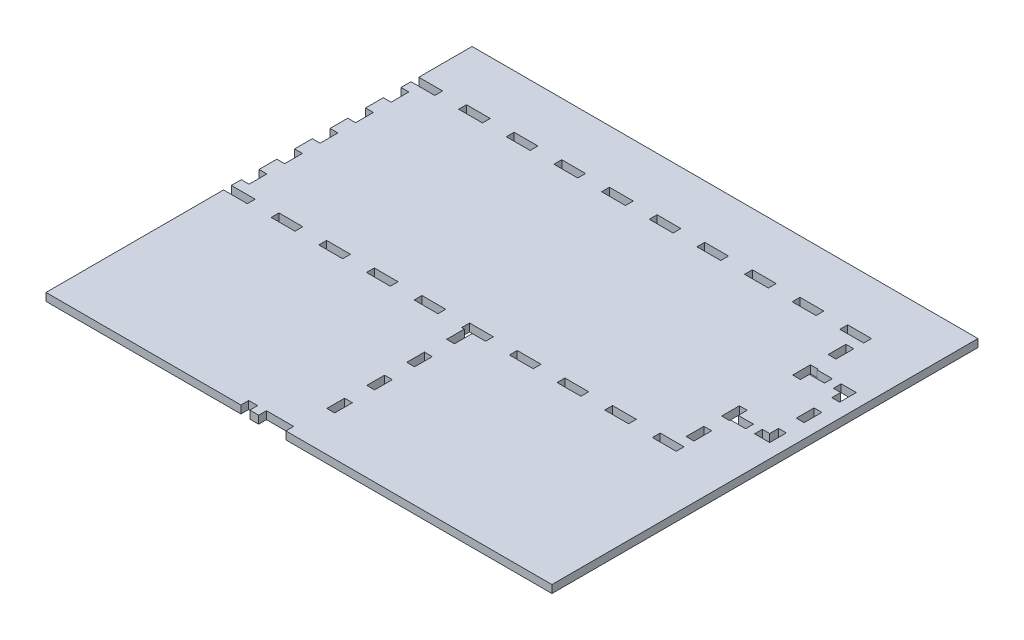
SolidWorks part; units mm, degrees
material "Acrylic (Medium-high impact)"
ref_plane "Front Plane" through (0, 0, 0) normal (0, 0, 1) x (1, 0, 0)
ref_plane "Top Plane" through (0, 0, 0) normal (0, 1, 0) x (1, 0, 0)
ref_plane "Right Plane" through (0, 0, 0) normal (1, 0, 0) x (0, 0, -1)
sketch "Sketch1" plane through (0, 0, 0) normal (0, 1, 0) x (1, 0, 0)
  line L1 (-161.925, 69.85) -> (161.925, 69.85)
  line L2 (-161.925, 69.85) -> (-161.925, -69.85)
  line L3 (-161.925, -69.85) -> (161.925, -69.85)
  line L4 (161.925, 69.85) -> (161.925, -69.85)
  point P4 (-161.925, 0)
  point P6 (0, 69.85)
  dimension "D1" = 139.7
  dimension "D2" = 323.85
extrude "Boss-Extrude1" add sketch "Sketch1" along normal blind 5.588
sketch "Sketch2" plane through (0, 5.588, 0) normal (0, 1, 0) x (1, 0, 0)
  line L0 (161.925, -69.85) -> (161.925, 69.85) construction
  line L1 (-161.925, 69.85) -> (161.925, 69.85)
  line L2 (-161.925, 69.85) -> (-161.925, -69.85)
  line L3 (-161.925, -69.85) -> (161.925, -69.85)
  line L4 (161.925, 69.85) -> (161.925, -69.85)
  line L5 (-161.925, -69.85) -> (161.925, -69.85) construction
  line L7 (-156.337, 64.262) -> (156.337, 64.262)
  line L8 (-156.337, 64.262) -> (-156.337, -64.262)
  line L9 (-156.337, -64.262) -> (156.337, -64.262)
  line L10 (156.337, 64.262) -> (156.337, -64.262)
  point P7 (-156.337, 0)
  point P14 (-161.925, 0)
  point P15 (0, -64.262)
  point P16 (0, -69.85)
  point P17 (156.337, 0)
  point P18 (161.925, 0)
  dimension "D1" = 5.588
  dimension "D2" = 5.588
extrude "Boss-Extrude2" add sketch "Sketch2" along normal blind 298.45
sketch "Sketch3" plane through (0, 0, 69.85) normal (0, 0, 1) x (1, 0, 0)
  line L0 (-51.435, 304.038) -> (-51.435, 0) construction
  line L2 (-156.337, 5.588) -> (156.337, 5.588) construction
  line L4 (-54.737, 282.448) -> (-54.737, 5.588)
  line L5 (-54.737, 5.588) -> (-48.133, 5.588)
  line L6 (-48.133, 291.592) -> (-48.133, 5.588)
  line L7 (-48.133, 291.592) -> (-67.691, 291.592)
  line L9 (-57.277, 284.988) -> (-67.691, 284.988)
  line L10 (-67.691, 291.592) -> (-67.691, 284.988)
  line L11 (-48.133, 101.6) -> (-35.433, 101.6) construction
  line L12 (-161.925, 0) -> (161.925, 0) construction
  line L13 (-38.608, 88.9) -> (-38.608, 101.6) construction
  line L14 (-41.783, 88.9) -> (-35.433, 88.9)
  line L15 (-41.783, 88.9) -> (-41.783, 71.9667)
  line L16 (-41.783, 71.9667) -> (-35.433, 71.9667)
  line L17 (-35.433, 88.9) -> (-35.433, 71.9667)
  line L18 (-41.783, 42.3333) -> (-35.433, 42.3333)
  line L19 (-41.783, 42.3333) -> (-41.783, 59.2667)
  line L20 (-41.783, 59.2667) -> (-35.433, 59.2667)
  line L21 (-35.433, 42.3333) -> (-35.433, 59.2667)
  line L26 (-41.783, 29.6333) -> (-35.433, 29.6333)
  line L27 (-41.783, 29.6333) -> (-41.783, 12.7)
  line L28 (-41.783, 12.7) -> (-35.433, 12.7)
  line L29 (-35.433, 29.6333) -> (-35.433, 12.7)
  line L30 (-38.608, 59.2667) -> (-38.608, 71.9667) construction
  line L31 (-38.608, 29.6333) -> (-38.608, 42.3333) construction
  line L32 (-38.608, 12.7) -> (-38.608, 0) construction
  line L33 (-161.925, 304.038) -> (161.925, 304.038) construction
  line L34 (-156.337, 304.038) -> (-156.337, 5.588) construction
  arc A0 (-54.737, 282.448) -> (-57.277, 284.988) centre (-57.277, 282.448) ccw
  point P5 (-51.435, 5.588)
  dimension "D5" = 2.54
  dimension "D1" = 6.604
  dimension "D2" = 12.954
  dimension "D3" = 6.604
  dimension "D4" = 286.004
  dimension "D6" = 101.6
  dimension "D7" = 12.7
  dimension "D8" = 12.7
  dimension "D9" = 6.35
  dimension "D10" = 101.6
extrude "Door Slot" cut sketch "Sketch3" against normal blind 12.7
sketch "Sketch4" plane through (0, 0, -64.262) normal (0, 0, 1) x (1, 0, 0)
  line L0 (-161.925, 304.038) -> (161.925, 304.038) construction
  line L1 (-74.041, 304.038) -> (-67.691, 304.038)
  line L2 (-74.041, 304.038) -> (-74.041, 5.588)
  line L3 (-74.041, 5.588) -> (-67.691, 5.588)
  line L4 (-67.691, 304.038) -> (-67.691, 5.588)
  line L5 (-44.958, 262.763) -> (-44.958, 246.888) construction
  line L6 (-67.691, 291.592) -> (-67.691, 284.988) construction
  line L7 (-48.133, 304.038) -> (-41.783, 304.038)
  line L8 (-48.133, 304.038) -> (-48.133, 5.588)
  line L9 (-48.133, 5.588) -> (-41.783, 5.588)
  line L10 (-41.783, 304.038) -> (-41.783, 5.588)
  line L11 (156.337, 5.588) -> (-156.337, 5.588) construction
  line L12 (-48.133, 5.588) -> (-48.133, 291.592) construction
  line L13 (-67.691, 304.038) -> (-74.041, 304.038)
  line L14 (-67.691, 304.038) -> (-67.691, 291.338)
  line L15 (-67.691, 291.338) -> (-74.041, 291.338)
  line L16 (-74.041, 304.038) -> (-74.041, 291.338)
  line L17 (-67.691, 275.463) -> (-74.041, 275.463)
  line L18 (-67.691, 275.463) -> (-67.691, 262.763)
  line L19 (-67.691, 262.763) -> (-74.041, 262.763)
  line L20 (-74.041, 275.463) -> (-74.041, 262.763)
  line L21 (-74.041, 5.588) -> (-67.691, 5.588)
  line L22 (-74.041, 5.588) -> (-74.041, 18.288)
  line L23 (-74.041, 18.288) -> (-67.691, 18.288)
  line L24 (-67.691, 5.588) -> (-67.691, 18.288)
  line L25 (-74.041, 34.163) -> (-67.691, 34.163)
  line L26 (-74.041, 34.163) -> (-74.041, 46.863)
  line L27 (-74.041, 46.863) -> (-67.691, 46.863)
  line L28 (-67.691, 34.163) -> (-67.691, 46.863)
  line L29 (-74.041, 91.313) -> (-67.691, 91.313)
  line L30 (-74.041, 91.313) -> (-74.041, 104.013)
  line L31 (-74.041, 104.013) -> (-67.691, 104.013)
  line L32 (-67.691, 91.313) -> (-67.691, 104.013)
  line L33 (-74.041, 148.463) -> (-67.691, 148.463)
  line L34 (-74.041, 148.463) -> (-74.041, 161.163)
  line L35 (-74.041, 161.163) -> (-67.691, 161.163)
  line L36 (-67.691, 148.463) -> (-67.691, 161.163)
  line L37 (-74.041, 177.038) -> (-67.691, 177.038)
  line L38 (-74.041, 177.038) -> (-74.041, 189.738)
  line L39 (-74.041, 189.738) -> (-67.691, 189.738)
  line L40 (-67.691, 177.038) -> (-67.691, 189.738)
  line L41 (-74.041, 205.613) -> (-67.691, 205.613)
  line L42 (-74.041, 205.613) -> (-74.041, 218.313)
  line L43 (-74.041, 218.313) -> (-67.691, 218.313)
  line L44 (-67.691, 205.613) -> (-67.691, 218.313)
  line L45 (-74.041, 234.188) -> (-67.691, 234.188)
  line L46 (-74.041, 234.188) -> (-74.041, 246.888)
  line L47 (-74.041, 246.888) -> (-67.691, 246.888)
  line L48 (-67.691, 234.188) -> (-67.691, 246.888)
  line L49 (-67.691, 132.588) -> (-74.041, 132.588)
  line L50 (-67.691, 132.588) -> (-67.691, 119.888)
  line L51 (-67.691, 119.888) -> (-74.041, 119.888)
  line L52 (-74.041, 132.588) -> (-74.041, 119.888)
  line L53 (-67.691, 75.438) -> (-74.041, 75.438)
  line L54 (-67.691, 75.438) -> (-67.691, 62.738)
  line L55 (-67.691, 62.738) -> (-74.041, 62.738)
  line L56 (-74.041, 75.438) -> (-74.041, 62.738)
  line L57 (-70.866, 304.038) -> (-70.866, 291.338) construction
  line L58 (-70.866, 291.338) -> (-70.866, 275.463) construction
  line L59 (-70.866, 275.463) -> (-70.866, 262.763) construction
  line L60 (-70.866, 246.888) -> (-70.866, 234.188) construction
  line L61 (-70.866, 234.188) -> (-70.866, 218.313) construction
  line L62 (-70.866, 218.313) -> (-70.866, 205.613) construction
  line L63 (-70.866, 205.613) -> (-70.866, 189.738) construction
  line L64 (-70.866, 189.738) -> (-70.866, 177.038) construction
  line L65 (-70.866, 177.038) -> (-70.866, 161.163) construction
  line L66 (-70.866, 161.163) -> (-70.866, 148.463) construction
  line L67 (-70.866, 132.588) -> (-70.866, 119.888) construction
  line L68 (-70.866, 119.888) -> (-70.866, 104.013) construction
  line L69 (-70.866, 104.013) -> (-70.866, 91.313) construction
  line L70 (-70.866, 91.313) -> (-70.866, 75.438) construction
  line L71 (-70.866, 75.438) -> (-70.866, 62.738) construction
  line L72 (-70.866, 62.738) -> (-70.866, 46.863) construction
  line L73 (-70.866, 46.863) -> (-70.866, 34.163) construction
  line L74 (-70.866, 34.163) -> (-70.866, 18.288) construction
  line L75 (-70.866, 18.288) -> (-70.866, 5.588) construction
  line L76 (-70.866, 148.463) -> (-70.866, 132.588) construction
  line L77 (-70.866, 262.763) -> (-70.866, 246.888) construction
  line L78 (-57.912, 304.038) -> (-57.912, 0) construction
  line L79 (161.925, 304.038) -> (-161.925, 304.038) construction
  line L80 (161.925, 0) -> (-161.925, 0) construction
  line L81 (-57.912, 8.3493) -> (-48.133, 8.3493) construction
  line L82 (-57.912, 8.3493) -> (-67.691, 8.3493) construction
  line L83 (-44.958, 148.463) -> (-44.958, 132.588) construction
  line L84 (-44.958, 18.288) -> (-44.958, 5.588) construction
  line L85 (-44.958, 34.163) -> (-44.958, 18.288) construction
  line L86 (-44.958, 46.863) -> (-44.958, 34.163) construction
  line L87 (-44.958, 62.738) -> (-44.958, 46.863) construction
  line L88 (-44.958, 75.438) -> (-44.958, 62.738) construction
  line L89 (-44.958, 91.313) -> (-44.958, 75.438) construction
  line L90 (-44.958, 104.013) -> (-44.958, 91.313) construction
  line L91 (-44.958, 119.888) -> (-44.958, 104.013) construction
  line L92 (-44.958, 132.588) -> (-44.958, 119.888) construction
  line L93 (-44.958, 161.163) -> (-44.958, 148.463) construction
  line L94 (-44.958, 177.038) -> (-44.958, 161.163) construction
  line L95 (-44.958, 189.738) -> (-44.958, 177.038) construction
  line L96 (-44.958, 205.613) -> (-44.958, 189.738) construction
  line L97 (-44.958, 218.313) -> (-44.958, 205.613) construction
  line L98 (-44.958, 234.188) -> (-44.958, 218.313) construction
  line L99 (-44.958, 246.888) -> (-44.958, 234.188) construction
  line L100 (-44.958, 275.463) -> (-44.958, 262.763) construction
  line L101 (-44.958, 291.338) -> (-44.958, 275.463) construction
  line L102 (-44.958, 304.038) -> (-44.958, 291.338) construction
  line L103 (-41.783, 75.438) -> (-41.783, 62.738)
  line L104 (-48.133, 62.738) -> (-41.783, 62.738)
  line L105 (-48.133, 75.438) -> (-48.133, 62.738)
  line L106 (-48.133, 75.438) -> (-41.783, 75.438)
  line L107 (-41.783, 132.588) -> (-41.783, 119.888)
  line L108 (-48.133, 119.888) -> (-41.783, 119.888)
  line L109 (-48.133, 132.588) -> (-48.133, 119.888)
  line L110 (-48.133, 132.588) -> (-41.783, 132.588)
  line L111 (-48.133, 234.188) -> (-48.133, 246.888)
  line L112 (-41.783, 246.888) -> (-48.133, 246.888)
  line L113 (-41.783, 234.188) -> (-41.783, 246.888)
  line L114 (-41.783, 234.188) -> (-48.133, 234.188)
  line L115 (-48.133, 205.613) -> (-48.133, 218.313)
  line L116 (-41.783, 218.313) -> (-48.133, 218.313)
  line L117 (-41.783, 205.613) -> (-41.783, 218.313)
  line L118 (-41.783, 205.613) -> (-48.133, 205.613)
  line L119 (-48.133, 177.038) -> (-48.133, 189.738)
  line L120 (-41.783, 189.738) -> (-48.133, 189.738)
  line L121 (-41.783, 177.038) -> (-41.783, 189.738)
  line L122 (-41.783, 177.038) -> (-48.133, 177.038)
  line L123 (-48.133, 148.463) -> (-48.133, 161.163)
  line L124 (-41.783, 161.163) -> (-48.133, 161.163)
  line L125 (-41.783, 148.463) -> (-41.783, 161.163)
  line L126 (-41.783, 148.463) -> (-48.133, 148.463)
  line L127 (-48.133, 91.313) -> (-48.133, 104.013)
  line L128 (-41.783, 104.013) -> (-48.133, 104.013)
  line L129 (-41.783, 91.313) -> (-41.783, 104.013)
  line L130 (-41.783, 91.313) -> (-48.133, 91.313)
  line L131 (-48.133, 34.163) -> (-48.133, 46.863)
  line L132 (-41.783, 46.863) -> (-48.133, 46.863)
  line L133 (-41.783, 34.163) -> (-41.783, 46.863)
  line L134 (-41.783, 34.163) -> (-48.133, 34.163)
  line L135 (-48.133, 5.588) -> (-48.133, 18.288)
  line L136 (-41.783, 18.288) -> (-48.133, 18.288)
  line L137 (-41.783, 5.588) -> (-41.783, 18.288)
  line L138 (-41.783, 5.588) -> (-48.133, 5.588)
  line L139 (-41.783, 275.463) -> (-41.783, 262.763)
  line L140 (-48.133, 262.763) -> (-41.783, 262.763)
  line L141 (-48.133, 275.463) -> (-48.133, 262.763)
  line L142 (-48.133, 275.463) -> (-41.783, 275.463)
  line L143 (-41.783, 304.038) -> (-41.783, 291.338)
  line L144 (-48.133, 291.338) -> (-41.783, 291.338)
  line L145 (-48.133, 304.038) -> (-48.133, 291.338)
  line L146 (-48.133, 304.038) -> (-41.783, 304.038)
  line L147 (-48.133, 304.038) -> (-48.133, 5.588)
  line L148 (-41.783, 5.588) -> (-48.133, 5.588)
  line L149 (-41.783, 304.038) -> (-41.783, 5.588)
  line L150 (-41.783, 304.038) -> (-48.133, 304.038)
  point P14 (-67.691, 288.29)
  dimension "D1" = 6.35
  dimension "D2" = 12.7
extrude "Door Guide Holes" cut sketch "Sketch4" against normal up to next (5.588 mm away) contours L17 L4 L15 L2 | L2 L47 L4 L19 | L45 L2 L43 L4 | L41 L2 L39 L4 | L37 L2 L35 L4 | L49 L4 L33 L2 | L4 L51 L2 L31 | L53 L4 L29 L2 | L4 L55 L2 L27 | L25 L2 L23 L4
ref_plane "Plane1" through (-57.912, 0, 0) normal (-1, 0, 0) x (0, 0, 1)
mirror "Mirror1" about plane through (-57.912, 0, 0) normal (-1, 0, 0) of "Door Guide Holes"
sketch "Lever Holes" plane through (0, 0, 69.85) normal (0, 0, 1) x (1, 0, 0)
  line L0 (49.276, 31.75) -> (58.928, 31.75)
  line L1 (49.276, 31.75) -> (49.276, 25.4)
  line L2 (49.276, 25.4) -> (58.928, 25.4)
  line L3 (58.928, 31.75) -> (58.928, 25.4)
  line L4 (36.1315, 19.05) -> (42.4815, 19.05)
  line L5 (36.1315, 19.05) -> (36.1315, 12.7)
  line L6 (36.1315, 12.7) -> (42.4815, 12.7)
  line L7 (42.4815, 19.05) -> (42.4815, 12.7)
  line L8 (65.7225, 19.05) -> (72.0725, 19.05)
  line L9 (65.7225, 19.05) -> (65.7225, 12.7)
  line L10 (65.7225, 12.7) -> (72.0725, 12.7)
  line L11 (72.0725, 19.05) -> (72.0725, 12.7)
  line L12 (42.4815, 15.875) -> (65.7225, 15.875) construction
  line L13 (-161.925, 0) -> (161.925, 0) construction
  line L14 (-48.133, 5.588) -> (156.337, 5.588) construction
  line L15 (156.337, 5.588) -> (-156.337, 5.588) construction
  point P12 (54.102, 15.875)
  point P13 (54.102, 25.4)
  point P24 (54.102, 5.588)
  dimension "D1" = 9.652
  dimension "D2" = 6.35
  dimension "D3" = 6.35
  dimension "D4" = 6.35
  dimension "D5" = 23.241
  dimension "D6" = 25.4
  dimension "D7" = 12.7
extrude "Cut-Extrude1" cut sketch "Lever Holes" against normal through all
sketch "Sketch7" plane through (161.925, 0, 0) normal (1, 0, 0) x (0, 0, -1)
  line L0 (-37.211, 92.583) -> (37.211, 92.583)
  line L1 (-37.211, 92.583) -> (-37.211, 18.161)
  line L2 (-37.211, 18.161) -> (37.211, 18.161)
  line L3 (37.211, 92.583) -> (37.211, 18.161)
  line L4 (-69.85, 0) -> (69.85, 0) construction
  circle A0 centre (0, 55.372) radius 26.9875
  circle A1 centre (-37.211, 92.583) radius 3.175
  circle A2 centre (37.211, 92.583) radius 3.175
  circle A3 centre (-37.211, 18.161) radius 3.175
  circle A4 centre (37.211, 18.161) radius 3.175
  point P9 (0, 18.161)
  point P10 (-37.211, 55.372)
  dimension "D3" = 53.975
  dimension "D4" = 6.35
  dimension "D1" = 74.422
  dimension "D2" = 55.372
extrude "Cut-Extrude2" cut sketch "Sketch7" against normal up to next contours A0 | L0 A1 L1 | L1 A1 L0 | L3 A2 L0 | L0 A2 L3 | L2 A3 L1 | L1 A3 L2 | L2 A4 L3 | L3 A4 L2
sketch "Sketch8" plane through (-161.925, 0, 0) normal (-1, 0, 0) x (0, 0, 1)
  line L0 (-69.85, 0) -> (69.85, 0) construction
  circle A0 centre (0, 19.05) radius 3.175
  point P6 (0, 0)
  dimension "D1" = 6.35
  dimension "D2" = 19.05
extrude "Cut-Extrude3" cut sketch "Sketch8" against normal up to next
sketch "Sketch10" plane through (0, 0, 0) normal (0, -1, 0) x (1, 0, 0)
  line L0 (-156.337, 64.262) -> (156.337, 64.262) construction
  line L1 (-161.925, 69.85) -> (-144.8803, 69.85)
  line L2 (-161.925, 69.85) -> (-161.925, 64.262)
  line L3 (-161.925, 64.262) -> (-144.8803, 64.262)
  line L4 (-144.8803, 69.85) -> (-144.8803, 64.262)
  line L5 (-144.8803, 69.85) -> (-127.8355, 69.85)
  line L6 (-144.8803, 69.85) -> (-144.8803, 64.262)
  line L7 (-144.8803, 64.262) -> (-127.8355, 64.262)
  line L8 (-127.8355, 69.85) -> (-127.8355, 64.262)
  line L9 (-127.8355, 69.85) -> (-110.7908, 69.85)
  line L10 (-127.8355, 69.85) -> (-127.8355, 64.262)
  line L11 (-127.8355, 64.262) -> (-110.7908, 64.262)
  line L12 (-110.7908, 69.85) -> (-110.7908, 64.262)
  line L13 (-110.7908, 69.85) -> (-93.7461, 69.85)
  line L14 (-110.7908, 69.85) -> (-110.7908, 64.262)
  line L15 (-110.7908, 64.262) -> (-93.7461, 64.262)
  line L16 (-93.7461, 69.85) -> (-93.7461, 64.262)
  line L17 (-161.925, 69.85) -> (161.925, 69.85) construction
  line L18 (-67.691, 64.262) -> (-48.133, 64.262) construction
  line L19 (-93.7461, 69.85) -> (-76.7013, 69.85)
  line L20 (-93.7461, 69.85) -> (-93.7461, 64.262)
  line L21 (-93.7461, 64.262) -> (-76.7013, 64.262)
  line L22 (-76.7013, 69.85) -> (-76.7013, 64.262)
  line L23 (-76.7013, 69.85) -> (-59.6566, 69.85)
  line L24 (-76.7013, 69.85) -> (-76.7013, 64.262)
  line L25 (-76.7013, 64.262) -> (-59.6566, 64.262)
  line L26 (-59.6566, 69.85) -> (-59.6566, 64.262)
  line L27 (-59.6566, 69.85) -> (-42.6118, 69.85)
  line L28 (-59.6566, 69.85) -> (-59.6566, 64.262)
  line L29 (-59.6566, 64.262) -> (-42.6118, 64.262)
  line L30 (-42.6118, 69.85) -> (-42.6118, 64.262)
  line L31 (-42.6118, 69.85) -> (-25.5671, 69.85)
  line L32 (-42.6118, 69.85) -> (-42.6118, 64.262)
  line L33 (-42.6118, 64.262) -> (-25.5671, 64.262)
  line L34 (-25.5671, 69.85) -> (-25.5671, 64.262)
  line L36 (-25.5671, 69.85) -> (-8.5224, 69.85)
  line L37 (-25.5671, 69.85) -> (-25.5671, 64.262)
  line L38 (-25.5671, 64.262) -> (-8.5224, 64.262)
  line L39 (-8.5224, 69.85) -> (-8.5224, 64.262)
  line L40 (-8.5224, 69.85) -> (8.5224, 69.85)
  line L41 (-8.5224, 69.85) -> (-8.5224, 64.262)
  line L42 (-8.5224, 64.262) -> (8.5224, 64.262)
  line L43 (8.5224, 69.85) -> (8.5224, 64.262)
  line L44 (8.5224, 69.85) -> (25.5671, 69.85)
  line L45 (8.5224, 69.85) -> (8.5224, 64.262)
  line L46 (8.5224, 64.262) -> (25.5671, 64.262)
  line L47 (25.5671, 69.85) -> (25.5671, 64.262)
  line L48 (25.5671, 69.85) -> (42.6118, 69.85)
  line L49 (25.5671, 69.85) -> (25.5671, 64.262)
  line L50 (25.5671, 64.262) -> (42.6118, 64.262)
  line L51 (42.6118, 69.85) -> (42.6118, 64.262)
  line L52 (42.6118, 69.85) -> (59.6566, 69.85)
  line L53 (42.6118, 69.85) -> (42.6118, 64.262)
  line L54 (42.6118, 64.262) -> (59.6566, 64.262)
  line L55 (59.6566, 69.85) -> (59.6566, 64.262)
  line L56 (59.6566, 69.85) -> (76.7013, 69.85)
  line L57 (59.6566, 69.85) -> (59.6566, 64.262)
  line L58 (59.6566, 64.262) -> (76.7013, 64.262)
  line L59 (76.7013, 69.85) -> (76.7013, 64.262)
  line L60 (76.7013, 69.85) -> (93.7461, 69.85)
  line L61 (76.7013, 69.85) -> (76.7013, 64.262)
  line L62 (76.7013, 64.262) -> (93.7461, 64.262)
  line L63 (93.7461, 69.85) -> (93.7461, 64.262)
  line L64 (93.7461, 69.85) -> (110.7908, 69.85)
  line L65 (93.7461, 69.85) -> (93.7461, 64.262)
  line L66 (93.7461, 64.262) -> (110.7908, 64.262)
  line L67 (110.7908, 69.85) -> (110.7908, 64.262)
  line L68 (110.7908, 69.85) -> (127.8355, 69.85)
  line L69 (110.7908, 69.85) -> (110.7908, 64.262)
  line L70 (110.7908, 64.262) -> (127.8355, 64.262)
  line L71 (127.8355, 69.85) -> (127.8355, 64.262)
  line L72 (127.8355, 69.85) -> (144.8803, 69.85)
  line L73 (127.8355, 69.85) -> (127.8355, 64.262)
  line L74 (127.8355, 64.262) -> (144.8803, 64.262)
  line L75 (144.8803, 69.85) -> (144.8803, 64.262)
  line L76 (-156.337, -64.262) -> (-156.337, 64.262) construction
  line L77 (-161.925, 69.85) -> (-156.337, 69.85)
  line L78 (-161.925, 69.85) -> (-161.925, 57.15)
  line L79 (-161.925, 57.15) -> (-156.337, 57.15)
  line L80 (-156.337, 69.85) -> (-156.337, 57.15)
  line L82 (-161.925, 57.15) -> (-156.337, 57.15)
  line L83 (-161.925, 57.15) -> (-161.925, 44.45)
  line L84 (-161.925, 44.45) -> (-156.337, 44.45)
  line L85 (-156.337, 57.15) -> (-156.337, 44.45)
  line L86 (-161.925, 44.45) -> (-156.337, 44.45)
  line L87 (-161.925, 44.45) -> (-161.925, 31.75)
  line L88 (-161.925, 31.75) -> (-156.337, 31.75)
  line L89 (-156.337, 44.45) -> (-156.337, 31.75)
  line L90 (-161.925, 31.75) -> (-156.337, 31.75)
  line L91 (-161.925, 31.75) -> (-161.925, 19.05)
  line L92 (-161.925, 19.05) -> (-156.337, 19.05)
  line L93 (-156.337, 31.75) -> (-156.337, 19.05)
  line L94 (-161.925, 19.05) -> (-156.337, 19.05)
  line L95 (-161.925, 19.05) -> (-161.925, 6.35)
  line L96 (-161.925, 6.35) -> (-156.337, 6.35)
  line L97 (-156.337, 19.05) -> (-156.337, 6.35)
  line L98 (-161.925, 6.35) -> (-156.337, 6.35)
  line L99 (-161.925, 6.35) -> (-161.925, -6.35)
  line L100 (-161.925, -6.35) -> (-156.337, -6.35)
  line L101 (-156.337, 6.35) -> (-156.337, -6.35)
  line L102 (-161.925, -6.35) -> (-156.337, -6.35)
  line L103 (-161.925, -6.35) -> (-161.925, -19.05)
  line L104 (-161.925, -19.05) -> (-156.337, -19.05)
  line L105 (-156.337, -6.35) -> (-156.337, -19.05)
  line L106 (-161.925, -19.05) -> (-156.337, -19.05)
  line L107 (-161.925, -19.05) -> (-161.925, -31.75)
  line L108 (-161.925, -31.75) -> (-156.337, -31.75)
  line L109 (-156.337, -19.05) -> (-156.337, -31.75)
  line L110 (-161.925, -31.75) -> (-156.337, -31.75)
  line L111 (-161.925, -31.75) -> (-161.925, -44.45)
  line L112 (-161.925, -44.45) -> (-156.337, -44.45)
  line L113 (-156.337, -31.75) -> (-156.337, -44.45)
  line L114 (-161.925, -44.45) -> (-156.337, -44.45)
  line L115 (-161.925, -44.45) -> (-161.925, -57.15)
  line L116 (-161.925, -57.15) -> (-156.337, -57.15)
  line L117 (-156.337, -44.45) -> (-156.337, -57.15)
  line L118 (161.925, 69.85) -> (161.925, -69.85) construction
  line L119 (144.8803, 69.85) -> (161.925, 69.85)
  line L120 (144.8803, 69.85) -> (144.8803, 64.262)
  line L121 (144.8803, 64.262) -> (161.925, 64.262)
  line L122 (161.925, 69.85) -> (161.925, 64.262)
  line L123 (161.925, -69.85) -> (-161.925, -69.85) construction
  line L124 (-161.925, -57.15) -> (-156.337, -57.15)
  line L125 (-161.925, -57.15) -> (-161.925, -69.85)
  line L126 (-161.925, -69.85) -> (-156.337, -69.85)
  line L127 (-156.337, -57.15) -> (-156.337, -69.85)
  line L128 (3.0734, 0) -> (-3.0734, 0) construction
  line L129 (161.925, -69.85) -> (161.925, -64.262)
  line L130 (144.8803, -64.262) -> (161.925, -64.262)
  line L131 (144.8803, -69.85) -> (161.925, -69.85)
  line L132 (144.8803, -69.85) -> (144.8803, -64.262)
  line L133 (127.8355, -64.262) -> (144.8803, -64.262)
  line L134 (127.8355, -69.85) -> (144.8803, -69.85)
  line L135 (127.8355, -69.85) -> (127.8355, -64.262)
  line L136 (110.7908, -64.262) -> (127.8355, -64.262)
  line L137 (110.7908, -69.85) -> (127.8355, -69.85)
  line L138 (110.7908, -69.85) -> (110.7908, -64.262)
  line L139 (93.7461, -64.262) -> (110.7908, -64.262)
  line L140 (93.7461, -69.85) -> (110.7908, -69.85)
  line L141 (93.7461, -69.85) -> (93.7461, -64.262)
  line L142 (76.7013, -64.262) -> (93.7461, -64.262)
  line L143 (76.7013, -69.85) -> (93.7461, -69.85)
  line L144 (59.6566, -64.262) -> (76.7013, -64.262)
  line L145 (76.7013, -69.85) -> (76.7013, -64.262)
  line L146 (59.6566, -69.85) -> (76.7013, -69.85)
  line L147 (59.6566, -69.85) -> (59.6566, -64.262)
  line L148 (42.6118, -64.262) -> (59.6566, -64.262)
  line L149 (42.6118, -69.85) -> (59.6566, -69.85)
  line L150 (42.6118, -69.85) -> (42.6118, -64.262)
  line L151 (25.5671, -64.262) -> (42.6118, -64.262)
  line L152 (25.5671, -69.85) -> (42.6118, -69.85)
  line L153 (25.5671, -69.85) -> (25.5671, -64.262)
  line L154 (8.5224, -69.85) -> (25.5671, -69.85)
  line L155 (8.5224, -64.262) -> (25.5671, -64.262)
  line L156 (8.5224, -69.85) -> (8.5224, -64.262)
  line L157 (-8.5224, -64.262) -> (8.5224, -64.262)
  line L158 (-8.5224, -69.85) -> (8.5224, -69.85)
  line L159 (-25.5671, -64.262) -> (-8.5224, -64.262)
  line L160 (-8.5224, -69.85) -> (-8.5224, -64.262)
  line L161 (-25.5671, -69.85) -> (-8.5224, -69.85)
  line L162 (-25.5671, -69.85) -> (-25.5671, -64.262)
  line L163 (-42.6118, -64.262) -> (-25.5671, -64.262)
  line L164 (-42.6118, -69.85) -> (-25.5671, -69.85)
  line L165 (-42.6118, -69.85) -> (-42.6118, -64.262)
  line L166 (-59.6566, -64.262) -> (-42.6118, -64.262)
  line L167 (-59.6566, -69.85) -> (-42.6118, -69.85)
  line L168 (-59.6566, -69.85) -> (-59.6566, -64.262)
  line L169 (-76.7013, -69.85) -> (-59.6566, -69.85)
  line L170 (-76.7013, -64.262) -> (-59.6566, -64.262)
  line L171 (-93.7461, -64.262) -> (-76.7013, -64.262)
  line L172 (-76.7013, -69.85) -> (-76.7013, -64.262)
  line L173 (-93.7461, -69.85) -> (-76.7013, -69.85)
  line L174 (-110.7908, -69.85) -> (-93.7461, -69.85)
  line L175 (-110.7908, -64.262) -> (-93.7461, -64.262)
  line L176 (-93.7461, -69.85) -> (-93.7461, -64.262)
  line L177 (-127.8355, -69.85) -> (-127.8355, -64.262)
  line L178 (-127.8355, -69.85) -> (-110.7908, -69.85)
  line L179 (-110.7908, -69.85) -> (-110.7908, -64.262)
  line L180 (-127.8355, -64.262) -> (-110.7908, -64.262)
  line L181 (-144.8803, -64.262) -> (-127.8355, -64.262)
  line L182 (-144.8803, -69.85) -> (-127.8355, -69.85)
  line L183 (-144.8803, -69.85) -> (-144.8803, -64.262)
  line L184 (-161.925, -69.85) -> (-144.8803, -69.85)
  line L185 (-161.925, -69.85) -> (-161.925, -64.262)
  line L186 (-161.925, -64.262) -> (-144.8803, -64.262)
  line L187 (0, -3.0734) -> (0, 3.0734) construction
  line L188 (161.925, -69.85) -> (156.337, -69.85)
  line L189 (156.337, -57.15) -> (156.337, -69.85)
  line L190 (161.925, -57.15) -> (161.925, -69.85)
  line L191 (161.925, -57.15) -> (156.337, -57.15)
  line L192 (156.337, -44.45) -> (156.337, -57.15)
  line L193 (161.925, -44.45) -> (161.925, -57.15)
  line L194 (161.925, -44.45) -> (156.337, -44.45)
  line L195 (156.337, -31.75) -> (156.337, -44.45)
  line L196 (161.925, -31.75) -> (161.925, -44.45)
  line L197 (161.925, -31.75) -> (156.337, -31.75)
  line L198 (161.925, -19.05) -> (161.925, -31.75)
  line L199 (156.337, -19.05) -> (156.337, -31.75)
  line L200 (156.337, -6.35) -> (156.337, -19.05)
  line L201 (161.925, -6.35) -> (161.925, -19.05)
  line L202 (161.925, -19.05) -> (156.337, -19.05)
  line L203 (161.925, -6.35) -> (156.337, -6.35)
  line L204 (156.337, 6.35) -> (156.337, -6.35)
  line L205 (161.925, 6.35) -> (161.925, -6.35)
  line L206 (161.925, 6.35) -> (156.337, 6.35)
  line L207 (156.337, 19.05) -> (156.337, 6.35)
  line L208 (161.925, 19.05) -> (161.925, 6.35)
  line L209 (161.925, 19.05) -> (156.337, 19.05)
  line L210 (161.925, 31.75) -> (156.337, 31.75)
  line L211 (161.925, 44.45) -> (156.337, 44.45)
  line L212 (161.925, 57.15) -> (156.337, 57.15)
  line L213 (156.337, 31.75) -> (156.337, 19.05)
  line L214 (161.925, 31.75) -> (161.925, 19.05)
  line L215 (156.337, 44.45) -> (156.337, 31.75)
  line L216 (161.925, 44.45) -> (161.925, 31.75)
  line L217 (156.337, 57.15) -> (156.337, 44.45)
  line L218 (161.925, 57.15) -> (161.925, 44.45)
  line L219 (156.337, 69.85) -> (156.337, 57.15)
  line L220 (161.925, 69.85) -> (161.925, 57.15)
  line M28 (-161.925, 69.85) -> (-161.925, -69.85)
  line M29 (-161.925, -69.85) -> (161.925, -69.85)
  line M30 (161.925, -69.85) -> (161.925, 69.85)
  line M31 (161.925, 69.85) -> (-161.925, 69.85)
sketch "Sketch9" plane through (0, 0, -69.85) normal (0, 0, -1) x (-1, 0, 0)
  line L0 (161.925, 304.038) -> (161.925, 0) construction
  line L1 (-161.925, 304.038) -> (161.925, 304.038)
  line L2 (-161.925, 304.038) -> (-161.925, 5.588)
  line L3 (-161.925, 5.588) -> (161.925, 5.588)
  line L4 (161.925, 304.038) -> (161.925, 5.588)
  line L5 (-156.337, 5.588) -> (156.337, 5.588) construction
extrude "Cut-Extrude4" cut sketch "Sketch9" against normal through all
extrude "Cut-Extrude6" cut sketch "Sketch10" against normal through all contours L80 L3 L4 M31 | L80 L1 L3 M28 | L12 L8 L11 M31 | L22 L16 L21 M31 | L30 L26 L29 M31 | L39 L34 L38 M31 | L47 L43 L46 M31 | L55 L51 L54 M31 | L63 L59 L62 M31 | L71 L67 L70 M31 | L219 L119 L75 L121 | L219 L121 M31 M30 | L212 L217 L211 M30 | L210 L213 L209 M30 | L202 L199 L197 M30 | L194 L192 L191 M30 | L130 L189 L131 M30 | L189 L130 L132 M29 | L138 L135 L136 M29 | L145 L141 L142 M29 | L150 L147 L148 M29 | L156 L153 L155 M29 | L162 L160 L159 M29 | L168 L165 L166 M29 | L176 L172 L171 M29 | L180 L177 L179 M29 | L186 L125 L127 M29 | L186 L127 L183 M29 | L117 L112 L116 M28 | L109 L104 L108 M28 | L101 L96 L100 M28 | L93 L88 L92 M28 | L85 L79 L84 M28
sketch "Sketch12" plane through (0, 0, 0) normal (0, -1, 0) x (-1, 0, 0)
  line L0 (161.925, -196.85) -> (161.925, -69.85)
  line L1 (161.925, -69.85) -> (-161.925, -69.85)
  line L2 (-161.925, -69.85) -> (-161.925, -196.85)
  line L3 (-161.925, -196.85) -> (161.925, -196.85)
  line L4 (-127.8355, -69.85) -> (-144.8803, -69.85) construction
  line L5 (-13.208, -139.7) -> (-13.208, -155.575) construction
  line L6 (-10.414, -69.85) -> (-16.002, -69.85)
  line L7 (-10.414, -69.85) -> (-10.414, -82.55)
  line L8 (-10.414, -82.55) -> (-16.002, -82.55)
  line L9 (-16.002, -69.85) -> (-16.002, -82.55)
  line L10 (-10.414, -98.425) -> (-16.002, -98.425)
  line L11 (-10.414, -98.425) -> (-10.414, -111.125)
  line L12 (-10.414, -111.125) -> (-16.002, -111.125)
  line L13 (-16.002, -98.425) -> (-16.002, -111.125)
  line L14 (-10.414, -127) -> (-16.002, -127)
  line L15 (-10.414, -127) -> (-10.414, -139.7)
  line L16 (-10.414, -139.7) -> (-16.002, -139.7)
  line L17 (-16.002, -127) -> (-16.002, -139.7)
  line L18 (-10.414, -155.575) -> (-16.002, -155.575)
  line L19 (-10.414, -155.575) -> (-10.414, -168.275)
  line L20 (-10.414, -168.275) -> (-16.002, -168.275)
  line L21 (-16.002, -155.575) -> (-16.002, -168.275)
  line L22 (-13.208, -82.55) -> (-13.208, -98.425) construction
  line L23 (-13.208, -111.125) -> (-13.208, -127) construction
  line L24 (127.8355, 69.85) -> (144.8803, 69.85) construction
  line L25 (-9.652, -196.85) -> (9.779, -196.85)
  line L26 (-9.652, -196.85) -> (-9.652, -191.262)
  line L27 (-9.652, -191.262) -> (9.779, -191.262)
  line L28 (9.779, -196.85) -> (9.779, -191.262)
  line L29 (16.129, -196.85) -> (22.479, -196.85)
  line L30 (16.129, -196.85) -> (16.129, -191.262)
  line L31 (16.129, -191.262) -> (22.479, -191.262)
  line L32 (22.479, -196.85) -> (22.479, -191.262)
  line L33 (161.925, 69.85) -> (-161.925, 69.85)
  line L34 (161.925, 69.85) -> (161.925, 107.95)
  line L35 (161.925, 107.95) -> (-161.925, 107.95)
  line L36 (-161.925, 69.85) -> (-161.925, 107.95)
  line L37 (-189.925, 107.95) -> (-189.925, -196.85) construction
  line L38 (-161.925, 107.95) -> (-200.025, 107.95)
  line L39 (-161.925, 107.95) -> (-161.925, -196.85)
  line L40 (-161.925, -196.85) -> (-200.025, -196.85)
  line L41 (-200.025, 107.95) -> (-200.025, -196.85)
  line L42 (0, 0) -> (-189.925, 0) construction
  line L43 (-128.8528, 0) -> (-128.8528, -30.988) construction
  line L44 (-128.8528, -30.988) -> (-189.925, -30.988) construction
  line L45 (-128.8528, 0) -> (-128.8528, 30.988) construction
  line L46 (-128.8528, 30.988) -> (-189.925, 30.988) construction
  line L60 (-177.131, -6.35) -> (-177.131, 6.35) construction
  line L63 (-187.131, -19.05) -> (-187.131, -6.35) construction
  line L64 (-179.1, 30.988) -> (-189.925, 30.988)
  line L66 (-179.1, 30.988) -> (-179.1, 25.4)
  line L67 (-179.1, 25.4) -> (-189.925, 25.4)
  line L68 (-189.925, 30.988) -> (-189.925, 25.4)
  line L69 (-179.1, -30.988) -> (-189.925, -30.988)
  line L70 (-179.1, -30.988) -> (-179.1, -25.4)
  line L71 (-179.1, -25.4) -> (-189.925, -25.4)
  line L72 (-189.925, -30.988) -> (-189.925, -25.4)
  line L73 (-161.925, -30.988) -> (-172.75, -30.988)
  line L74 (-161.925, -30.988) -> (-161.925, -25.4)
  line L75 (-161.925, -25.4) -> (-172.75, -25.4)
  line L76 (-172.75, -30.988) -> (-172.75, -25.4)
  line L77 (-161.925, 30.988) -> (-172.75, 30.988)
  line L78 (-161.925, 30.988) -> (-161.925, 25.4)
  line L79 (-161.925, 25.4) -> (-172.75, 25.4)
  line L80 (-172.75, 30.988) -> (-172.75, 25.4)
  line L81 (-189.925, -19.05) -> (-184.337, -19.05)
  line L82 (-189.925, -19.05) -> (-189.925, -30.988)
  line L83 (-189.925, -30.988) -> (-184.337, -30.988)
  line L84 (-184.337, -19.05) -> (-184.337, -30.988)
  line L85 (-189.925, 6.35) -> (-184.337, 6.35)
  line L86 (-189.925, 6.35) -> (-189.925, -6.35)
  line L87 (-189.925, -6.35) -> (-184.337, -6.35)
  line L88 (-184.337, 6.35) -> (-184.337, -6.35)
  line L89 (-189.925, 19.05) -> (-184.337, 19.05)
  line L90 (-189.925, 19.05) -> (-189.925, 30.988)
  line L91 (-189.925, 30.988) -> (-184.337, 30.988)
  line L92 (-184.337, 19.05) -> (-184.337, 30.988)
  line L93 (-187.131, 6.35) -> (-187.131, 19.05) construction
  point P63 (-177.131, 0)
  point P83 (-184.8119, -5.2992)
  dimension "D1" = 127
  dimension "D2" = 15.875
  dimension "D3" = 145.923
  dimension "D4" = 5.588
  dimension "D5" = 12.7
  dimension "D6" = 6.35
  dimension "D7" = 19.431
  dimension "D8" = 5.588
  dimension "D9" = 6.35
  dimension "D10" = 6.35
  dimension "D11" = 38.1
  dimension "D12" = 38.1
  dimension "D13" = 28
  dimension "D14" = 30.988
  dimension "D15" = 5.588
  dimension "D16" = 10.825
  dimension "D17" = 12.7
  dimension "D18" = 5.588
extrude "Boss-Extrude3" add sketch "Sketch12" against normal up to surface (5.588 mm away) contours L9 L1 L2 L3 L0 L7 L8 L21 L18 L19 L20 L17 L14 L15 L16 L13 L10 L11 L12 | L36 L33 L34 L35 | L38 L41 L40 L2 L39 L36
